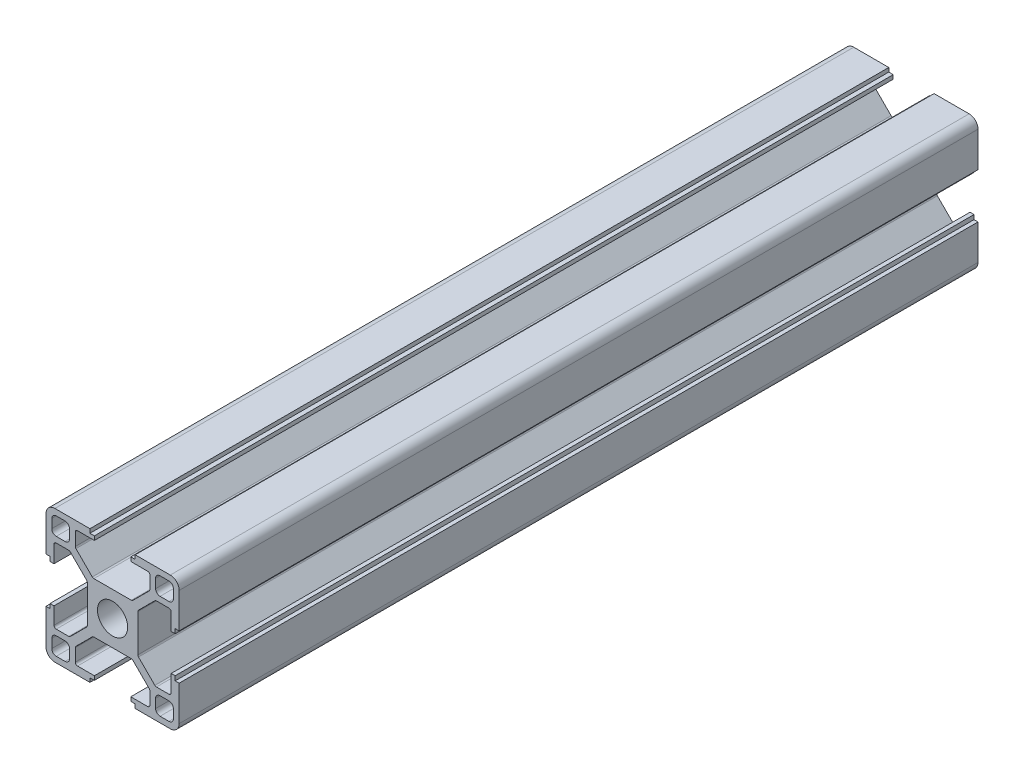
SolidWorks part; units mm, degrees
ref_plane "前视基准面" through (0, 0, 0) normal (0, 0, 1) x (1, 0, 0)
ref_plane "上视基准面" through (0, 0, 0) normal (0, 1, 0) x (1, 0, 0)
ref_plane "右视基准面" through (0, 0, 0) normal (1, 0, 0) x (0, 0, -1)
sketch "草图1" plane through (0, 0, 0) normal (0, 0, 1) x (1, 0, 0)
  line L0 (0, 0) -> (0, 65.3905) construction
  line L1 (0, 0) -> (64.2648, 0) construction
  line L2 (0, 0) -> (79.9729, 79.9729) construction
  line L3 (5.7, 0) -> (5.7, 4.4272)
  line L4 (5.7, 4.4272) -> (9.6728, 8.4)
  line L5 (9.6728, 8.4) -> (13.2, 8.4)
  line L6 (13.2, 8.4) -> (13.2, 4.1)
  line L7 (13.2, 4.1) -> (14.1, 4.1)
  line L8 (14.1, 4.1) -> (14.1, 5.1)
  line L9 (14.1, 5.1) -> (15, 5.1)
  line L10 (15, 5.1) -> (15, 15)
  line L11 (5.1, 15) -> (15, 15)
  line L12 (5.1, 14.1) -> (5.1, 15)
  line L13 (4.1, 14.1) -> (5.1, 14.1)
  line L14 (4.1, 13.2) -> (4.1, 14.1)
  line L15 (8.4, 13.2) -> (4.1, 13.2)
  line L16 (8.4, 9.6728) -> (8.4, 13.2)
  line L17 (4.4272, 5.7) -> (8.4, 9.6728)
  line L18 (0, 5.7) -> (4.4272, 5.7)
  line L20 (9.7, 9.7) -> (13.7, 9.7)
  line L21 (9.7, 9.7) -> (9.7, 13.7)
  line L22 (9.7, 13.7) -> (13.7, 13.7)
  line L23 (13.7, 9.7) -> (13.7, 13.7)
  line L24 (9.7, 9.7) -> (13.7, 13.7) construction
  line L25 (9.7, 13.7) -> (13.7, 9.7) construction
  line L26 (0, 5.7) -> (0, 0)
  line L27 (0, 0) -> (5.7, 0)
  point P9 (11.7, 11.7)
  dimension "D1" = 45
  dimension "D2" = 5.7
  dimension "D3" = 1.8
  dimension "D4" = 0.9
  dimension "D5" = 8.2
  dimension "D6" = 10.2
  dimension "D7" = 1.8
  dimension "D8" = 15
  dimension "D9" = 16.8
  dimension "D10" = 4
  dimension "D11" = 1.3
extrude "凸台-拉伸1" add sketch "草图1" along normal blind 180 contours L3 L4 L5 L6 L7 L8 L9 L10 L11 L12 L13 L14 L15 L16 L17 L18 L26 L27
fillet "圆角1" radius 1 4 edges at (9.7, 9.7, 90) (13.7, 9.7, 90) (9.7, 13.7, 90) (13.7, 13.7, 90)
fillet "圆角2" radius 2 1 edges at (15, 15, 90)
fillet "圆角3" radius 0.5 6 edges at (5.7, 4.4272, 90) (4.4272, 5.7, 90) (8.4, 13.2, 90) (8.4, 9.6728, 90) (9.6728, 8.4, 90) (13.2, 8.4, 90)
pattern_circular "阵列(圆周)1" count 4 over 360 about axis through (0, 0, 0) along (0, 0, 1) of "圆角2", "圆角3", "凸台-拉伸1", "圆角1"
sketch "草图2" plane through (0, 0, 180) normal (0, 0, 1) x (1, 0, 0)
  circle A0 centre (0, 0) radius 3.4
  dimension "D1" = 6.8
extrude "切除-拉伸1" cut sketch "草图2" against normal through all
cosmetic thread "装饰螺纹线1" parameters "D1"=20, "D2"=8
sketch "草图3" plane through (0, 0, 0) normal (1, 0, 0) x (0, 0, -1)
  line L0 (-8.5, 60.2652) -> (-8.5, -70.1349) construction
  line L1 (-318.169, 0) -> (51.4974, 0) construction
  line L2 (0, -5.1) -> (0, -13) construction
  circle A0 centre (-8.5, 0) radius 3.05
  circle A1 centre (-71.5, 0) radius 3.05
  dimension "D1" = 6.1
  dimension "D3" = 71.5
  dimension "D2" = 8.5
extrude "切除-拉伸2" cut sketch "草图3" against normal mid plane 20
